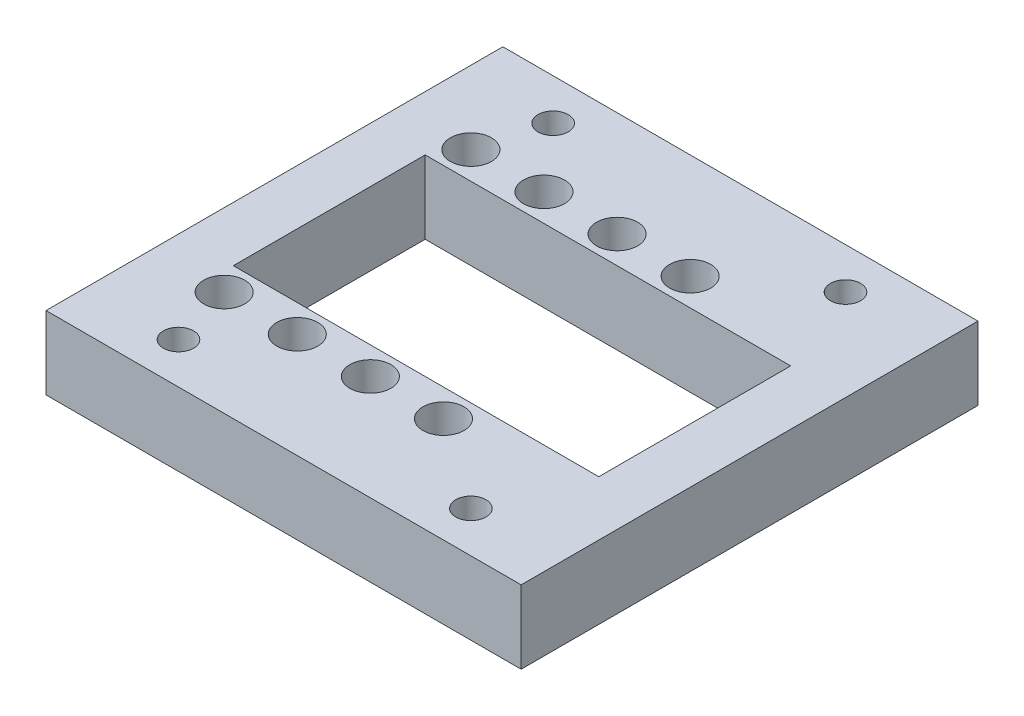
SolidWorks part; units mm, degrees
ref_plane "Front Plane" through (0, 0, 0) normal (0, 0, 1) x (1, 0, 0)
ref_plane "Top Plane" through (0, 0, 0) normal (0, 1, 0) x (1, 0, 0)
ref_plane "Right Plane" through (0, 0, 0) normal (1, 0, 0) x (0, 0, -1)
sketch "Sketch1" plane through (0, 0, 0) normal (0, 1, 0) x (1, 0, 0)
  line L0 (0, 13.5) -> (0, -13.5) construction
  line L1 (0, 0) -> (18, 0) construction
  line L2 (0, 13.5) -> (35.0352, 13.5) construction
  line L3 (18, 0) -> (18, 25)
  line L4 (44, -25) -> (-8, -25)
  line L5 (44, -25) -> (44, 25)
  line L6 (44, 25) -> (-8, 25)
  line L7 (-8, -25) -> (-8, 25)
  line L8 (44, -25) -> (-8, 25) construction
  line L9 (44, 25) -> (-8, -25) construction
  line L14 (-2, 10.5) -> (38, 10.5)
  line L15 (-2, 10.5) -> (-2, -10.5)
  line L16 (-2, -10.5) -> (38, -10.5)
  line L17 (38, 10.5) -> (38, -10.5)
  line L18 (-2, 10.5) -> (38, -10.5) construction
  line L19 (-2, -10.5) -> (38, 10.5) construction
  circle A0 centre (0, 13.5) radius 1.125
  circle A1 centre (8, 13.5) radius 1.125
  circle A2 centre (16, 13.5) radius 1.125
  circle A3 centre (24, 13.5) radius 1.125
  circle A4 centre (24, -13.5) radius 1.125
  circle A5 centre (16, -13.5) radius 1.125
  circle A6 centre (8, -13.5) radius 1.125
  circle A7 centre (0, -13.5) radius 1.125
  circle A8 centre (34, 20.5) radius 1.65
  circle A9 centre (2, 20.5) radius 1.65
  circle A10 centre (34, -20.5) radius 1.65
  circle A11 centre (2, -20.5) radius 1.65
  point P3 (18, 0)
  point P4 (0, 0)
  dimension "D2" = 2.25
  dimension "D3" = 2.25
  dimension "D4" = 2.25
  dimension "D5" = 2.25
  dimension "D16" = 3.3
  dimension "D1" = 27
  dimension "D6" = 8
  dimension "D7" = 8
  dimension "D8" = 8
  dimension "D9" = 21
  dimension "D10" = 2
  dimension "D11" = 40
  dimension "D12" = 50
  dimension "D13" = 52
  dimension "D14" = 6
  dimension "D15" = 20.5
  dimension "D17" = 10
extrude "Boss-Extrude1" add sketch "Sketch1" along normal blind 8
sketch "Sketch2" plane through (0, 8, 0) normal (0, 1, 0) x (1, 0, 0)
  line L0 (-8, 0) -> (44, 0)
  line L1 (-8, -25) -> (-8, 25) construction
  line L2 (44, -25) -> (44, 25) construction
  circle A0 centre (0, 13.5) radius 2.25
  circle A1 centre (8, 13.5) radius 2.25
  circle A2 centre (16, 13.5) radius 2.25
  circle A3 centre (24, 13.5) radius 2.25
  circle A4 centre (24, -13.5) radius 2.25
  circle A5 centre (16, -13.5) radius 2.25
  circle A6 centre (8, -13.5) radius 2.25
  circle A7 centre (0, -13.5) radius 2.25
  circle M13 centre (8, -13.5) radius 1.125
  circle M14 centre (24, -13.5) radius 1.125
  circle M15 centre (24, 13.5) radius 1.125
  circle M16 centre (16, 13.5) radius 1.125
  circle M17 centre (8, 13.5) radius 1.125
  circle M18 centre (0, 13.5) radius 1.125
  circle M23 centre (16, -13.5) radius 1.125
  circle M24 centre (0, -13.5) radius 1.125
  dimension "D1" = 4.5
  dimension "D2" = 4.5
  dimension "D3" = 4.5
  dimension "D4" = 4.5
extrude "Cut-Extrude1" cut sketch "Sketch2" against normal blind 3.5 contours A0 M18 | A1 M17 | A2 M16 | A3 M15 | A4 M14 | A5 M23 | A6 M13 | A7 M24
